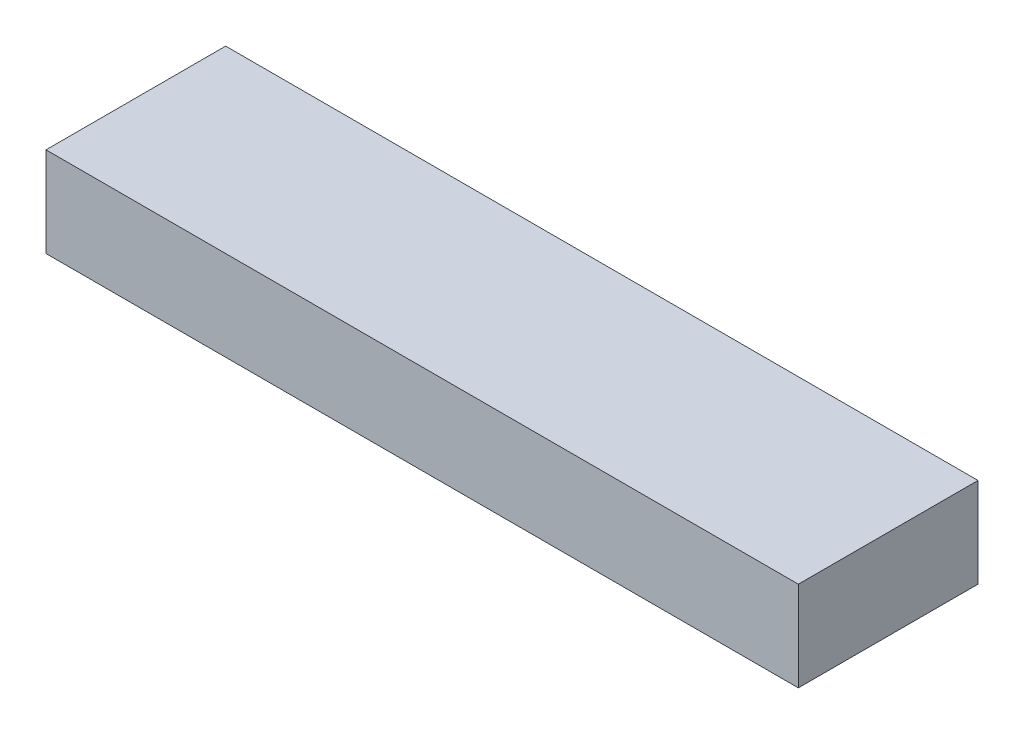
SolidWorks part; units mm, degrees
ref_plane "Front Plane" through (0, 0, 0) normal (0, 0, 1) x (1, 0, 0)
ref_plane "Top Plane" through (0, 0, 0) normal (0, 1, 0) x (1, 0, 0)
ref_plane "Right Plane" through (0, 0, 0) normal (1, 0, 0) x (0, 0, -1)
sketch "Sketch1" plane through (0, 0, 0) normal (0, 1, 0) x (1, 0, 0)
  line L1 (-212.725, -50.8) -> (212.725, -50.8)
  line L2 (-212.725, -50.8) -> (-212.725, 50.8)
  line L3 (-212.725, 50.8) -> (212.725, 50.8)
  line L4 (212.725, -50.8) -> (212.725, 50.8)
  line L5 (-212.725, -50.8) -> (212.725, 50.8) construction
  line L6 (-212.725, 50.8) -> (212.725, -50.8) construction
  point P0 (0, 0)
  dimension "D1" = 425.45
  dimension "D2" = 101.6
extrude "Boss-Extrude1" add sketch "Sketch1" along normal mid plane 50.8
